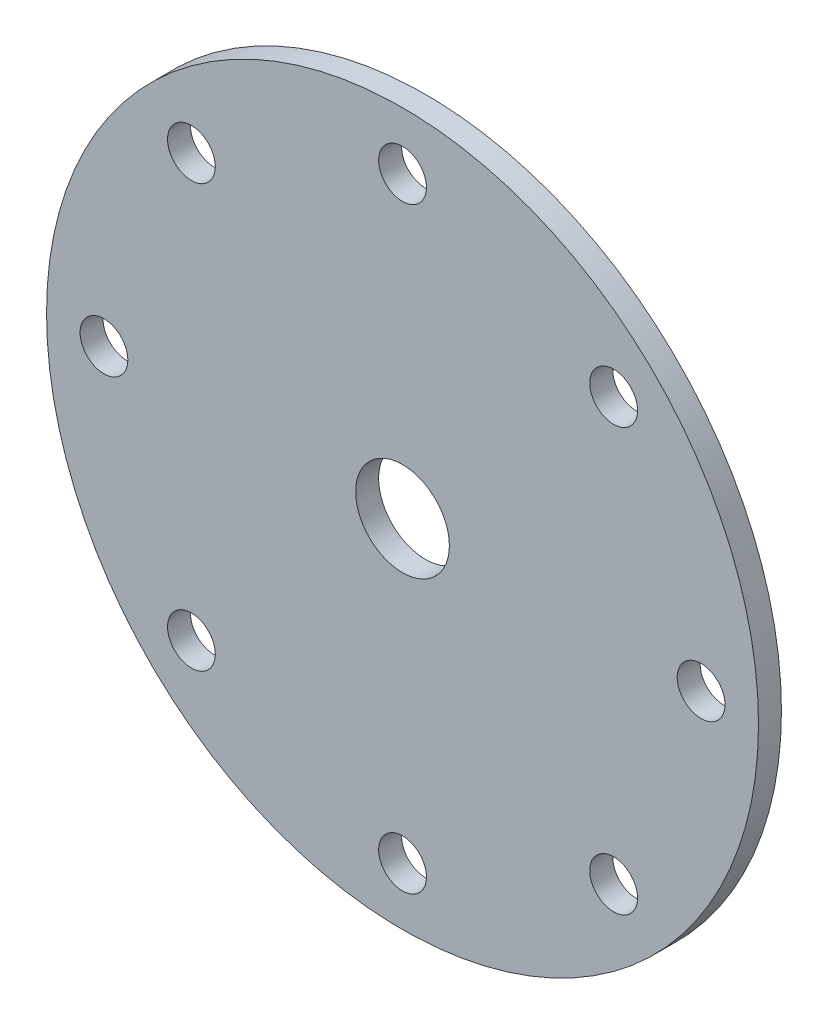
SolidWorks part; units mm, degrees
material "Plain Carbon Steel"
ref_plane "Front Plane" through (0, 0, 0) normal (0, 0, 1) x (1, 0, 0)
ref_plane "Top Plane" through (0, 0, 0) normal (0, 1, 0) x (1, 0, 0)
ref_plane "Right Plane" through (0, 0, 0) normal (1, 0, 0) x (0, 0, -1)
sketch "Sketch1" plane through (0, 0, 0) normal (0, 0, 1) x (1, 0, 0)
  line L0 (0, 98.425) -> (0, -98.425) construction
  line L1 (-98.425, 0) -> (98.425, 0) construction
  line L2 (-58.3717, 58.3717) -> (58.3717, -58.3717) construction
  line L3 (-58.3717, -58.3717) -> (58.3717, 58.3717) construction
  circle A0 centre (0, 0) radius 98.425
  circle A1 centre (0, 0) radius 12.954
  circle A2 centre (0, 82.55) radius 6.604
  circle A6 centre (58.3717, 58.3717) radius 6.604
  circle A7 centre (82.55, 0) radius 6.604
  circle A8 centre (58.3717, -58.3717) radius 6.604
  circle A9 centre (0, -82.55) radius 6.604
  circle A10 centre (-58.3717, -58.3717) radius 6.604
  circle A11 centre (-82.55, 0) radius 6.604
  circle A12 centre (-58.3717, 58.3717) radius 6.604
  dimension "D1" = 196.85
  dimension "D2" = 25.908
  dimension "D3" = 13.208
  dimension "D6" = 82.55
  dimension "D4" = 82.55
  dimension "D5" = 8
extrude "Rotor Disc" add sketch "Sketch1" along normal blind 6.35
